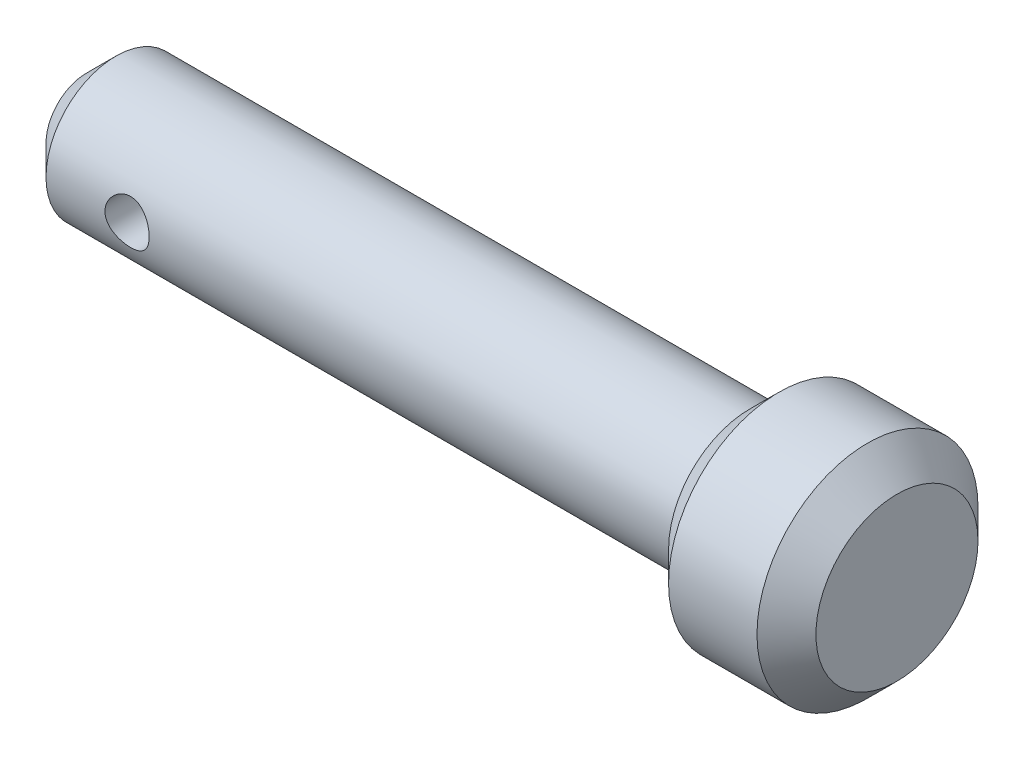
SolidWorks part; units mm, degrees
ref_plane "Alzado" through (0, 0, 0) normal (0, 0, 1) x (1, 0, 0)
ref_plane "Planta" through (0, 0, 0) normal (0, 1, 0) x (1, 0, 0)
ref_plane "Vista lateral" through (0, 0, 0) normal (1, 0, 0) x (0, 0, -1)
sketch "Sketch1" plane through (0, 0, 0) normal (0, 0, 1) x (1, 0, 0)
  line L0 (0, 0) -> (0, -9.5)
  line L1 (0, -9.5) -> (90, -9.5)
  line L2 (90, -9.5) -> (90, -15)
  line L3 (90, -15) -> (110, -15)
  line L4 (0, 0) -> (110, 0)
  line L5 (110, 0) -> (110, -15)
  dimension "D1" = 110
  dimension "D2" = 15
  dimension "D3" = 20
  dimension "D4" = 9.5
revolve "Revolve1" add sketch "Sketch1" angle 360 about L4
chamfer "Chamfer1" distance 4 angle 45 3 edges at (0, 0, 9.5) (90, 0, 15) (110, 0, 15)
sketch "Sketch2" plane through (0, 0, 0) normal (0, 0, 1) x (1, 0, 0)
  line L0 (90, 0) -> (4, 0) construction
  line L1 (0, 5.5) -> (0, -5.5) construction
  circle A0 centre (15, 0) radius 3
  dimension "D1" = 6
  dimension "D2" = 15
extrude "Cut-Extrude1" cut sketch "Sketch2" against normal through all and the other way through all
